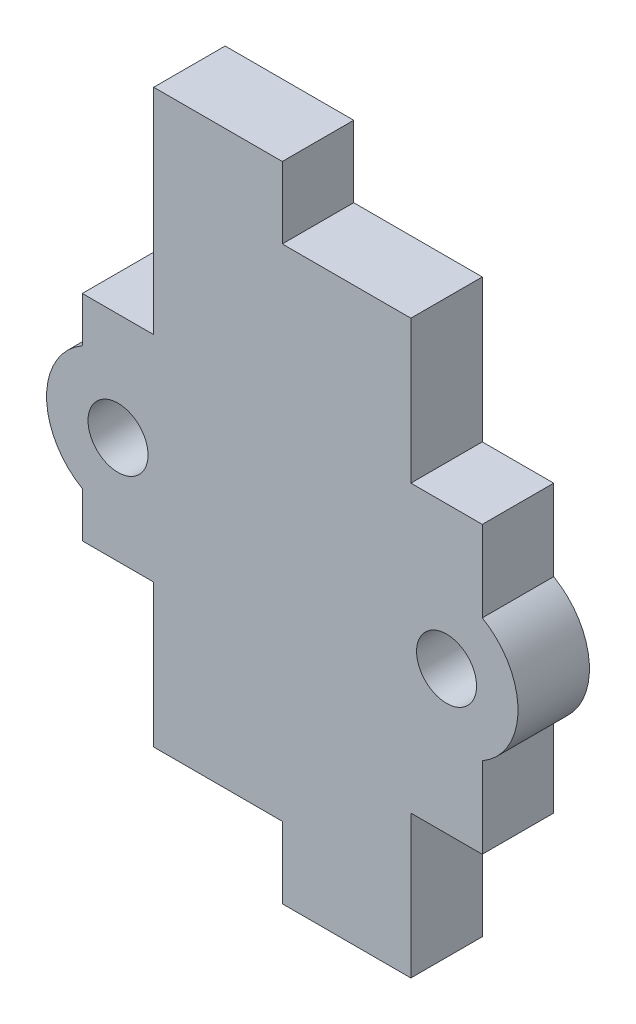
SolidWorks part; units mm, degrees
ref_plane "Front Plane" through (0, 0, 0) normal (0, 0, 1) x (1, 0, 0)
ref_plane "Top Plane" through (0, 0, 0) normal (0, 1, 0) x (1, 0, 0)
ref_plane "Right Plane" through (0, 0, 0) normal (1, 0, 0) x (0, 0, -1)
sketch "Sketch1" plane through (0, 0, 0) normal (0, 0, 1) x (1, 0, 0)
  line L1 (0, 0) -> (-18, 0)
  line L2 (0, 0) -> (0, 35)
  line L3 (0, 35) -> (-18, 35)
  line L4 (-18, 0) -> (-18, 35)
  dimension "D1" = 18
  dimension "D2" = 35
extrude "Boss-Extrude1" add sketch "Sketch1" along normal blind 5
sketch "Sketch2" plane through (0, 0, 0) normal (1, 0, 0) x (0, 0, -1)
  line L0 (-5, 0) -> (-5, 35) construction
  line L1 (-5, 5) -> (0, 5)
  line L2 (-5, 5) -> (-5, 25)
  line L3 (-5, 25) -> (0, 25)
  line L4 (0, 5) -> (0, 25)
  line L5 (0, 0) -> (0, 35) construction
  line L7 (-5, 35) -> (0, 35) construction
  dimension "D1" = 10
  dimension "D2" = 30
extrude "Boss-Extrude2" add sketch "Sketch2" along normal blind 5
sketch "Sketch3" plane through (0, 0, 0) normal (0, -1, 0) x (1, 0, 0)
  line L0 (-18, 0) -> (0, 0) construction
  line L1 (0, 5) -> (-9, 5)
  line L2 (0, 5) -> (0, 0)
  line L3 (0, 0) -> (-9, 0)
  line L4 (-9, 5) -> (-9, 0)
extrude "Boss-Extrude3" add sketch "Sketch3" along normal blind 5
sketch "Sketch4" plane through (0, 0, 5) normal (0, 0, 1) x (1, 0, 0)
  line L0 (-18, 35) -> (-18, 0) construction
  line L1 (-18, 10) -> (-23, 10)
  line L2 (-18, 10) -> (-18, 25)
  line L3 (-18, 25) -> (-23, 25)
  line L4 (-23, 10) -> (-23, 25)
  line L5 (0, 35) -> (-18, 35) construction
  dimension "D1" = 5
  dimension "D2" = 15
  dimension "D3" = 10
extrude "Boss-Extrude4" add sketch "Sketch4" against normal blind 5
sketch "Sketch5" plane through (0, 35, 0) normal (0, 1, 0) x (1, 0, 0)
  line L0 (0, -5) -> (-18, -5) construction
  line L1 (-18, 0) -> (-9, 0)
  line L2 (-18, 0) -> (-18, -5)
  line L3 (-18, -5) -> (-9, -5)
  line L4 (-9, 0) -> (-9, -5)
extrude "Boss-Extrude5" add sketch "Sketch5" along normal blind 5
sketch "Sketch6" plane through (0, 0, 0) normal (0, 0, -1) x (-1, 0, 0)
  line L0 (-5, 25) -> (0, 25) construction
  line L1 (-5, 5) -> (-5, 25) construction
  circle A0 centre (-2.5, 15) radius 2.1
  dimension "D1" = 4.2
  dimension "D2" = 10
  dimension "D3" = 2.5
extrude "Cut-Extrude1" cut sketch "Sketch6" against normal blind 5
sketch "Sketch7" plane through (0, 0, 0) normal (0, 0, -1) x (-1, 0, 0)
  line L0 (-5, 5) -> (-5, 25) construction
  line L1 (-5, 10.6699) -> (-5, 19.3301)
  arc A0 (-5, 10.6699) -> (-5, 19.3301) centre (-2.5, 15) cw
  dimension "D1" = 5
extrude "Boss-Extrude6" add sketch "Sketch7" against normal blind 5
sketch "Sketch8" plane through (0, 0, 5) normal (0, 0, 1) x (1, 0, 0)
  line L0 (-18, 25) -> (-23, 25) construction
  line L1 (-23, 25) -> (-23, 10) construction
  circle A0 centre (-20.5, 17.5) radius 2.1
  circle A1 centre (-4.5, -2.5) radius 2.1
  circle A2 centre (-13.5, 37.5) radius 2.1
  dimension "D1" = 4.2
  dimension "D2" = 7.5
  dimension "D3" = 2.5
  dimension "D4" = 4.2
  dimension "D5" = 4.2
extrude "Cut-Extrude2" cut sketch "Sketch8" against normal blind 5 contours A0 | A1 | A2
sketch "Sketch9" plane through (0, 0, 5) normal (0, 0, 1) x (1, 0, 0)
  line L2 (-23, 25) -> (-23, 10) construction
  line L3 (-23, 21.8301) -> (-23, 13.1699)
  arc A1 (-23, 13.1699) -> (-23, 21.8301) centre (-20.5, 17.5) cw
  line M17 (-23, 25) -> (-23, 10)
  dimension "D2" = 5
extrude "Boss-Extrude7" add sketch "Sketch9" against normal blind 5 contours A1 M17
